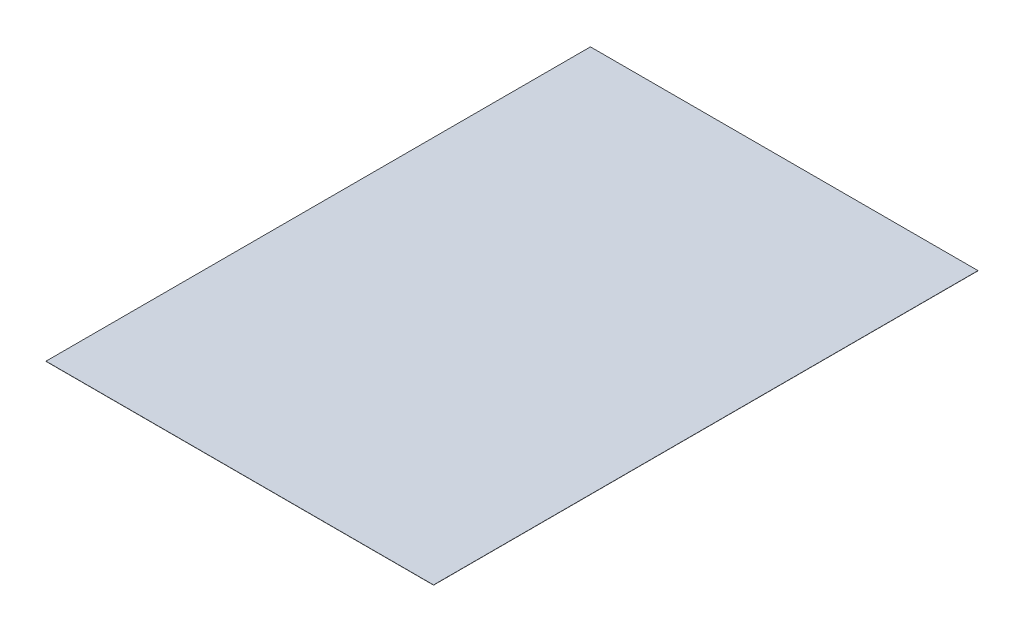
SolidWorks part; units mm, degrees
ref_plane "Front plane" through (0, 0, 0) normal (0, 0, 1) x (1, 0, 0)
ref_plane "Top plane" through (0, 0, 0) normal (0, 1, 0) x (1, 0, 0)
ref_plane "Right Plane" through (0, 0, 0) normal (1, 0, 0) x (0, 0, -1)
sketch "Sketch1" plane through (0, 0, 0) normal (0, 1, 0) x (1, 0, 0)
  line L1 (0, 0) -> (210, 0)
  line L2 (0, 0) -> (0, 295)
  line L3 (0, 295) -> (210, 295)
  line L4 (210, 0) -> (210, 295)
  dimension "D1" = 210
  dimension "D2" = 295
extrude "Boss-Extrude1" add sketch "Sketch1" along normal blind 0.1
